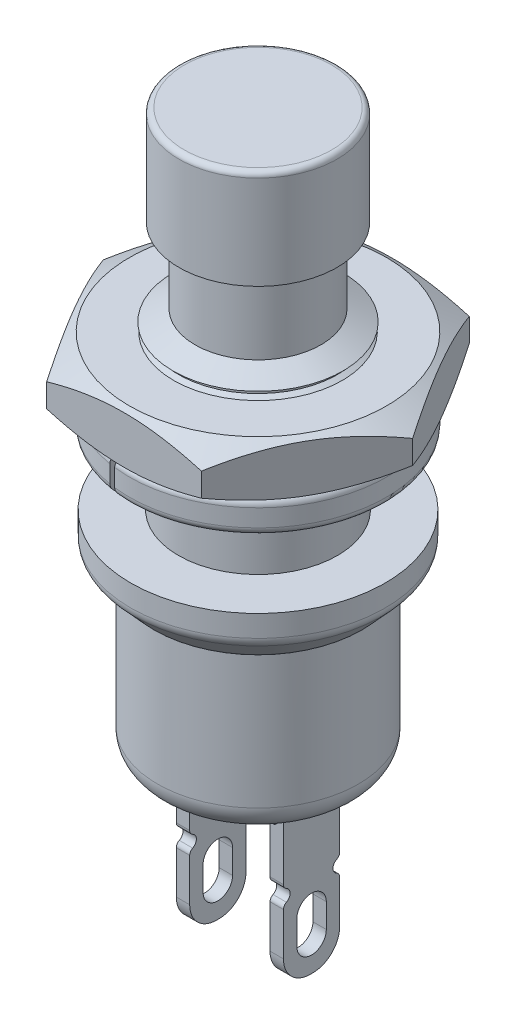
SolidWorks part; units mm, degrees
material "Plain Carbon Steel"
ref_plane "Front Plane" through (0, 0, 0) normal (0, 0, 1) x (1, 0, 0)
ref_plane "Top Plane" through (0, 0, 0) normal (0, 1, 0) x (1, 0, 0)
ref_plane "Right Plane" through (0, 0, 0) normal (1, 0, 0) x (0, 0, -1)
sketch "Sketch1" plane through (0, 0, 0) normal (0, 0, 1) x (1, 0, 0)
  line L0 (0, 0) -> (0, -2)
  line L1 (0, -2) -> (3.75, -2)
  line L2 (0, 0) -> (4.75, 0)
  line L3 (4.75, 0) -> (4.75, -0.8063)
  line L4 (4.6195, -1.1432) -> (3.8978, -1.9347)
  arc A0 (4.75, -0.8063) -> (4.6195, -1.1432) centre (4.25, -0.8063) cw
  arc A1 (3.75, -2) -> (3.8978, -1.9347) centre (3.75, -1.8) ccw
  point P8 (4.75, -1)
  point P11 (3.8383, -2)
  dimension "D5" = 0.5
  dimension "D6" = 0.2
  dimension "D1" = 2
  dimension "D2" = 4.75
  dimension "D3" = 1
  dimension "D4" = 3.75
revolve "Revolve1" add sketch "Sketch1" angle 360 about L0
sketch "Sketch3" plane through (0, -2, 0) normal (0, -1, 0) x (1, 0, 0)
  circle A1 centre (0, 0) radius 3.75
  circle A2 centre (0, 0) radius 3.75
  dimension "D1" = 0
extrude "Boss-Extrude1" add sketch "Sketch3" along normal blind 6
fillet "Fillet1" radius 1 1 edges at (0, -8, -3.75)
sketch "Sketch4" plane through (0, 0, 0) normal (0, 0, 1) x (1, 0, 0)
  line L0 (0, 0) -> (0, 10.5)
  line L1 (0, 0) -> (0, -8) construction
  line L2 (-2.75, -8) -> (2.75, -8) construction
  line L3 (0, 10.5) -> (2.35, 10.5)
  line L4 (2.35, 10.5) -> (2.35, 6.5)
  line L5 (0, 0) -> (2.97, 0)
  line L7 (3.3, 1.4) -> (3.3, 6)
  line L8 (2.35, 6.5) -> (3.3, 6)
  line L9 (2.97, 0) -> (2.97, 1.4)
  line L10 (2.97, 1.4) -> (3.3, 1.4)
  dimension "D1" = 2.35
  dimension "D2" = 3.3
  dimension "D3" = 1.4
  dimension "D4" = 6.5
  dimension "D5" = 10.5
  dimension "D6" = 2.97
  dimension "D7" = 6
revolve "Revolve2" add sketch "Sketch4" angle 360 about L1
sketch "Sketch5" plane through (0, 0, 0) normal (0, 0, 1) x (1, 0, 0)
  line L0 (0, 0) -> (0, 1.4) construction
  line L1 (4.75, 0) -> (-4.75, 0) construction
  line L2 (-2.97, 1.4) -> (2.97, 1.4) construction
  line L3 (0, 1.4) -> (2.97, 1.4) construction
  line L4 (2.97, 1.4) -> (3.3164, 1.4) construction
  line L5 (3.3164, 1.4) -> (3.8164, 1.4) construction
  line L6 (3.8164, 1.65) -> (3.8164, 1.15)
  line L7 (3.3164, 1.65) -> (3.3164, 1.15) construction
  line L8 (3.8164, 1.65) -> (3.3164, 1.65)
  line L11 (3.3164, 1.15) -> (3.8164, 1.15)
  line L12 (2.97, 1.45) -> (2.97, 1.35)
  line L13 (2.97, 1.45) -> (3.3164, 1.65)
  line L14 (2.97, 1.35) -> (3.3164, 1.15)
  line L15 (-3.3, 1.4) -> (3.3, 1.4) construction
  line L16 (2.97, 0) -> (2.97, 1.4) construction
  dimension "D1" = 0.5
  dimension "D2" = 0.1
  dimension "D3" = 60
revolve "Cut-Revolve1" cut sketch "Sketch5" angle 360 about L0
pattern_linear "LPattern1" count 10 spacing 0.5 along (0, 1, 0) of "Cut-Revolve1"
sketch "Sketch6" plane through (0, 10.5, 0) normal (0, 1, 0) x (1, 0, 0)
  circle A0 centre (0, 0) radius 1.75
  dimension "D1" = 3.5
extrude "Cut-Extrude1" cut sketch "Sketch6" against normal blind 10
sketch "Sketch7" plane through (0, -8, 0) normal (0, -1, 0) x (1, 0, 0)
  line L0 (-1.75, 0) -> (1.75, 0) construction
  line L6 (1.5, -1.375) -> (2, -1.375)
  line L7 (1.5, -1.375) -> (1.5, 1.375)
  line L8 (1.5, 1.375) -> (2, 1.375)
  line L9 (2, -1.375) -> (2, 1.375)
  line L10 (1.5, -1.375) -> (2, 1.375) construction
  line L11 (1.5, 1.375) -> (2, -1.375) construction
  line L12 (-1.5, -1.375) -> (-2, -1.375)
  line L13 (-1.5, -1.375) -> (-1.5, 1.375)
  line L14 (-1.5, 1.375) -> (-2, 1.375)
  line L15 (-2, -1.375) -> (-2, 1.375)
  line L16 (-1.5, -1.375) -> (-2, 1.375) construction
  line L17 (-1.5, 1.375) -> (-2, -1.375) construction
  dimension "D1" = 3.5
  dimension "D2" = 2.75
  dimension "D3" = 0.5
extrude "Boss-Extrude2" add sketch "Sketch7" along normal blind 0.5
sketch "Sketch8" plane through (0, -8.5, 0) normal (0, -1, 0) x (1, 0, 0)
  line L0 (-1.75, 1.375) -> (-1.75, -1.375) construction
  line L1 (-1.5, 1.375) -> (-2, 1.375) construction
  line L2 (-2, -1.375) -> (-1.5, -1.375) construction
  line L3 (1.75, 1.375) -> (1.75, -1.375) construction
  line L4 (2, 1.375) -> (1.5, 1.375) construction
  line L5 (1.5, -1.375) -> (2, -1.375) construction
  line L6 (-2, 1.375) -> (-2, -1.375) construction
  line L7 (-1.5, 1.05) -> (-2, 1.05)
  line L8 (-1.5, 1.05) -> (-1.5, -1.05)
  line L9 (-1.5, -1.05) -> (-2, -1.05)
  line L10 (-2, 1.05) -> (-2, -1.05)
  line L11 (-1.5, 1.05) -> (-2, -1.05) construction
  line L12 (-1.5, -1.05) -> (-2, 1.05) construction
  line L13 (2, -1.375) -> (2, 1.375) construction
  line L14 (1.5, 1.05) -> (2, 1.05)
  line L15 (1.5, 1.05) -> (1.5, -1.05)
  line L16 (1.5, -1.05) -> (2, -1.05)
  line L17 (2, 1.05) -> (2, -1.05)
  line L18 (1.5, 1.05) -> (2, -1.05) construction
  line L19 (1.5, -1.05) -> (2, 1.05) construction
  point P12 (-1.75, 0)
  point P19 (1.75, 0)
  dimension "D1" = 2.1
extrude "Boss-Extrude3" add sketch "Sketch8" along normal blind 5.5
sketch "Sketch9" plane through (2, 0, 0) normal (1, 0, 0) x (0, 0, -1)
  line L0 (0, -14) -> (0, -11) construction
  line L1 (1.05, -14) -> (-1.05, -14) construction
  line L2 (-1.05, -11) -> (1.05, -11) construction
  line L3 (-1.05, -14) -> (-1.05, -8.5) construction
  circle A0 centre (-1.05, -11) radius 0.25
  circle A1 centre (1.05, -11) radius 0.25
  dimension "D2" = 0.5
  dimension "D1" = 3
extrude "Cut-Extrude2" cut sketch "Sketch9" against normal up to surface (4 mm away) up to face at (-2, -9.75, 0)
sketch "Sketch10" plane through (2, 0, 0) normal (1, 0, 0) x (0, 0, -1)
  line L0 (0, -14) -> (0, -13.4) construction
  line L1 (1.05, -14) -> (-1.05, -14) construction
  line L2 (0, -11.95) -> (0, -12.85) construction
  line L3 (0.55, -11.95) -> (0.55, -12.85)
  line L4 (-0.55, -11.95) -> (-0.55, -12.85)
  line L5 (0, -12.85) -> (0, -13.4) construction
  line L6 (0, -11.95) -> (0, -11.4) construction
  line L7 (0, -12.4) -> (-0.55, -12.4) construction
  line L8 (-0.55, -12.4) -> (-1.05, -12.4) construction
  line L9 (-1.05, -14) -> (-1.05, -11.25) construction
  line L10 (0, -12.4) -> (0.55, -12.4) construction
  line L11 (0.55, -12.4) -> (1.05, -12.4) construction
  line L12 (1.05, -14) -> (1.05, -11.25) construction
  arc A0 (0.55, -11.95) -> (-0.55, -11.95) centre (0, -11.95) ccw
  arc A1 (-0.55, -12.85) -> (0.55, -12.85) centre (0, -12.85) ccw
  point P7 (0, -12.4)
  dimension "D1" = 0.5
  dimension "D2" = 2
  dimension "D3" = 0.6
extrude "Cut-Extrude3" cut sketch "Sketch10" against normal up to surface (4 mm away) up to face at (-2, -10.1667, 0)
fillet "Fillet2" radius 0.2 8 edges at (-1.75, -11.25, 1.05) (-1.75, -10.75, 1.05) (-1.75, -10.75, -1.05) (-1.75, -11.25, -1.05) (1.75, -10.75, -1.05) (1.75, -11.25, -1.05) (1.75, -11.25, 1.05) (1.75, -10.75, 1.05)
fillet "Fillet3" radius 1 4 edges at (-1.75, -14, -1.05) (-1.75, -14, 1.05) (1.75, -14, 1.05) (1.75, -14, -1.05)
ref_plane "SET NUT GAP" through (0, 2.5, 0) normal (0, 1, 0) x (1, 0, 0)
sketch "Sketch12" plane through (0, 2.5, 0) normal (0, 1, 0) x (1, 0, 0)
  circle A0 centre (0, 0) radius 4.8
  circle A1 centre (0, 0) radius 3.55
  dimension "D1" = 9.6
  dimension "D2" = 1.25
extrude "Boss-Extrude4" add sketch "Sketch12" along normal blind 1.25 separate body
sketch "Sketch13" plane through (0, 3.75, 0) normal (0, 1, 0) x (1, 0, 0)
  line L0 (0, 0) -> (0, -3.55) construction
  line L1 (0, -3.55) -> (-0.6927, -4.7498) construction
  line L2 (-0.1144, -3.5482) -> (-0.7985, -4.7331)
  line L3 (0.1166, -3.5481) -> (-0.5855, -4.7642)
  circle A0 centre (0, 0) radius 3.55 construction
  arc A1 (-0.1144, -3.5482) -> (0.1166, -3.5481) centre (0, 0) ccw
  circle A2 centre (0, 0) radius 4.8 construction
  arc A3 (-0.7985, -4.7331) -> (-0.5855, -4.7642) centre (0, 0) ccw
  dimension "D1" = 150
  dimension "D2" = 0.1
  dimension "D3" = 0.1
extrude "Cut-Extrude4" cut sketch "Sketch13" against normal up to surface (1.25 mm away) up to face at (0, 2.5, 4.8)
fillet "Fillet5" radius 0.3 4 edges at (-0.0011, 2.5, -3.55) (-0.0011, 3.75, -3.55) (0.6922, 2.5, -4.7498) (0.6922, 3.75, -4.7498)
sketch "Sketch14" plane through (0, 3.75, 0) normal (0, 1, 0) x (1, 0, 0)
  line L1 (5.7735, 0) -> (2.8868, 5)
  line L2 (2.8868, 5) -> (-2.8868, 5)
  line L3 (-2.8868, 5) -> (-5.7735, 0)
  line L4 (-5.7735, 0) -> (-2.8868, -5)
  line L5 (-2.8868, -5) -> (2.8868, -5)
  line L6 (2.8868, -5) -> (5.7735, 0)
  circle A0 centre (0, 0) radius 5 construction
  circle A1 centre (0, 0) radius 3.15
  dimension "D1" = 10
  dimension "D2" = 6.3
extrude "Boss-Extrude5" add sketch "Sketch14" along normal blind 2 separate body
sketch "Sketch15" plane through (0, 0, 0) normal (0, 0, 1) x (1, 0, 0)
  line L0 (0, 0) -> (0, 3.75) construction
  line L1 (-2.8868, 3.75) -> (2.8868, 3.75) construction
  line L2 (0, 3.75) -> (0, 5.75) construction
  line L3 (-2.8868, 5.75) -> (2.8868, 5.75) construction
  line L4 (0, 5.75) -> (4.8, 5.75) construction
  line L5 (2.8868, 5.75) -> (5.7735, 5.75) construction
  line L6 (4.8, 5.75) -> (4.8, 3.75) construction
  line L7 (2.8868, 3.75) -> (5.7735, 3.75) construction
  line L8 (4.8, 3.75) -> (0, 3.75) construction
  line L9 (4.8, 5.75) -> (5.7735, 5.75)
  line L10 (5.7735, 5.75) -> (5.7735, 5.1879)
  line L11 (5.7735, 5.75) -> (5.7735, 3.75) construction
  line L12 (5.7735, 5.1879) -> (4.8, 5.75)
  line L13 (4.8, 3.75) -> (5.7735, 3.75)
  line L14 (5.7735, 3.75) -> (5.7735, 4.3121)
  line L15 (5.7735, 4.3121) -> (4.8, 3.75)
  dimension "D1" = 30
  dimension "D2" = 4.8
revolve "Cut-Revolve2" cut sketch "Sketch15" angle 360 about L2
sketch "Sketch19" plane through (0, 0, 0) normal (0, 0, 1) x (1, 0, 0)
  line L0 (0, 5.2) -> (0, -7.8)
  line L1 (0, -7.8) -> (0, -8) construction
  line L2 (-2.75, -8) -> (2.75, -8) construction
  line L3 (0, 5.2) -> (2.5, 5.2)
  line L4 (2.5, 5.2) -> (2.5, -0.3)
  line L5 (2.5, -0.3) -> (4.2, -0.3)
  line L6 (4.2, -0.3) -> (4.2, -1)
  line L7 (4.2, -1) -> (3.1, -2.2)
  line L8 (3.1, -2.2) -> (3.1, -6.8)
  line L9 (2.1, -7.8) -> (0, -7.8)
  arc A0 (3.1, -6.8) -> (2.1, -7.8) centre (2.1, -6.8) cw
  dimension "D8" = 1
  dimension "D1" = 0.2
  dimension "D2" = 5.6
  dimension "D3" = 1.2
  dimension "D4" = 1.7
  dimension "D5" = 2.5
  dimension "D6" = 3.1
  dimension "D7" = 7.5
  dimension "D9" = 13
revolve "Real-World Weight Adjustment" cut sketch "Sketch19" angle 360 about L1
sketch "Sketch 19.5 Down 21 Up" plane through (0, 0, 0) normal (0, 0, 1) x (1, 0, 0)
  line L0 (0, 0) -> (0, 4) construction
  line L1 (0, 12) -> (0, 13) construction
  line L2 (1.45, 4) -> (1.75, 4)
  line L3 (0, 4) -> (0, 12) construction
  line L4 (1.45, 12) -> (1.75, 12)
  line L5 (1.75, 4) -> (1.75, 12)
  line L6 (0, 13) -> (1.75, 13) construction
  line L7 (1.75, 13) -> (1.75, 12) construction
  line L8 (0, 0) -> (0, -8) construction
  line L9 (-2.75, -8) -> (2.75, -8) construction
  line L10 (1.45, 12) -> (1.45, 4)
  line L11 (1.45, 12) -> (0, 12) construction
  line L12 (1.45, 4) -> (0, 4) construction
  dimension "D1" = 8
  dimension "D2" = 1
  dimension "D3" = 1.75
  dimension "D4" = 21
  dimension "D5" = 0.3
revolve "SWITCH 19.5 Down 21 Up" add sketch "Sketch 19.5 Down 21 Up" angle 360 about L3
sketch "Sketch21" plane through (0, 0, 0) normal (0, 0, 1) x (1, 0, 0)
  line L0 (0, 13) -> (0, 12)
  line L6 (2.95, 9.3) -> (2.95, 12.8)
  line L7 (2.75, 13) -> (0, 13)
  line L8 (2.95, 9.3) -> (2.35, 9.3)
  line L9 (2.35, 9.3) -> (2.35, 12)
  line L10 (2.35, 12) -> (0, 12)
  line L11 (2.35, 6.5) -> (2.35, 10.5) construction
  arc A0 (2.95, 12.8) -> (2.75, 13) centre (2.75, 12.8) ccw
  dimension "D3" = 0.2
  dimension "D1" = 3.7
  dimension "D2" = 2.95
revolve "Red Cap" add sketch "Sketch21" angle 360 about L1
